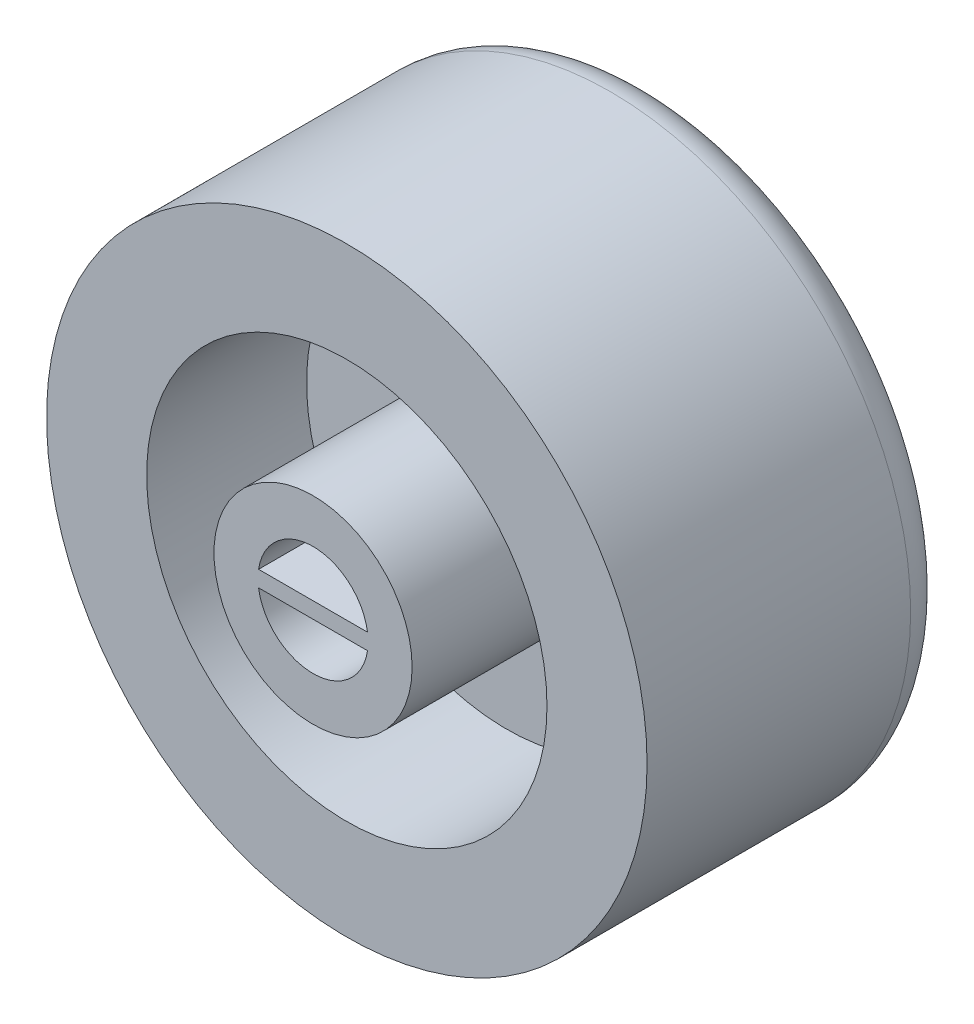
SolidWorks part; units mm, degrees
ref_plane "Front Plane" through (0, 0, 0) normal (0, 0, 1) x (1, 0, 0)
ref_plane "Top Plane" through (0, 0, 0) normal (0, 1, 0) x (1, 0, 0)
ref_plane "Right Plane" through (0, 0, 0) normal (1, 0, 0) x (0, 0, -1)
sketch "Sketch1" plane through (0, 0, 0) normal (0, 1, 0) x (1, 0, 0)
  line L0 (2.75, 40.6021) -> (2.75, 53.6021)
  line L1 (2.75, 53.6021) -> (0, 53.6021)
  line L2 (0, -55) -> (0, 55) construction
  line L3 (0, 53.6021) -> (0, 58.6021)
  line L4 (0, 58.6021) -> (15, 57.2898)
  line L5 (15, 57.2898) -> (15, 42.2898)
  line L6 (15, 42.2898) -> (10, 42.2898)
  line L7 (10, 42.2898) -> (10, 50.2782)
  line L8 (10, 50.2782) -> (4.95, 50.2782)
  line L9 (4.95, 50.2782) -> (4.95, 40.6021)
  line L10 (4.95, 40.6021) -> (2.75, 40.6021)
  dimension "D1" = 2.75
  dimension "D2" = 15
  dimension "D3" = 4.95
  dimension "D4" = 10
  dimension "D5" = 13
  dimension "D6" = 15
  dimension "D7" = 5
  dimension "D8" = 95
revolve "Revolve1" add sketch "Sketch1" angle 360 about L3
fillet "Fillet1" radius 2 1 edges at (15, 0, -57.2898)
ref_plane "Plane1" through (15, 0, 0) normal (1, 0, 0) x (0, 0, -1)
sketch "Sketch5" plane through (0, 0, -53.6021) normal (0, 0, 1) x (1, 0, 0)
  line L0 (9.9, 0) -> (-9.9, 0) construction
  line L1 (-3.0012, 0.4) -> (2.9039, 0.4)
  line L2 (-3.0012, 0.4) -> (-3.0012, -0.4)
  line L3 (-3.0012, -0.4) -> (2.9039, -0.4)
  line L4 (2.9039, 0.4) -> (2.9039, -0.4)
  dimension "D1" = 0.8
  dimension "D2" = 0.4
extrude "Boss-Extrude4" add sketch "Sketch5" along normal blind 13
